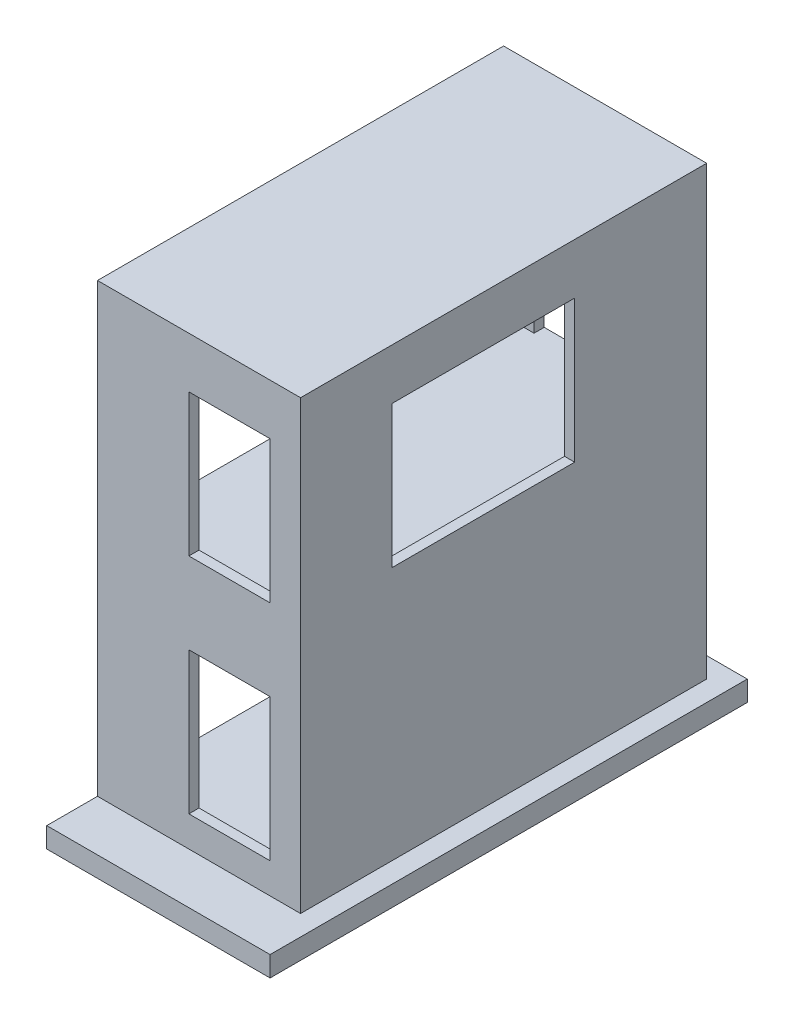
SolidWorks part; units mm, degrees
ref_plane "Front Plane" through (0, 0, 0) normal (0, 0, 1) x (1, 0, 0)
ref_plane "Top Plane" through (0, 0, 0) normal (0, 1, 0) x (1, 0, 0)
ref_plane "Right Plane" through (0, 0, 0) normal (1, 0, 0) x (0, 0, -1)
sketch "Sketch1" plane through (0, 0, 0) normal (0, 1, 0) x (1, 0, 0)
  line L1 (-60, -117.5) -> (60, -117.5)
  line L2 (-60, -117.5) -> (-60, 117.5)
  line L3 (-60, 117.5) -> (60, 117.5)
  line L4 (60, -117.5) -> (60, 117.5)
  line L5 (-60, -117.5) -> (60, 117.5) construction
  line L6 (-60, 117.5) -> (60, -117.5) construction
  point P0 (0, 0)
  dimension "D1" = 235
  dimension "D2" = 120
extrude "floor" add sketch "Sketch1" along normal blind 10
sketch "Sketch2" plane through (0, 10, 0) normal (0, 1, 0) x (1, 0, 0)
  line L0 (-50, 107.5) -> (50, 107.5) construction
  line L1 (-50, 102.5) -> (45, 102.5) construction
  line L2 (50, 107.5) -> (50, -92.5) construction
  line L3 (45, 102.5) -> (45, -87.5) construction
  line L4 (50, -92.5) -> (35, -92.5) construction
  line L5 (-5, -92.5) -> (-50, -92.5) construction
  line L6 (45, -87.5) -> (35, -87.5) construction
  line L7 (-5, -87.5) -> (-50, -87.5) construction
  line L8 (45, -87.5) -> (35, -87.5) construction
  line L9 (35, -87.5) -> (35, -92.5) construction
  line L10 (-5, -92.5) -> (-5, -87.5) construction
  line L11 (-50, -92.5) -> (50, 107.5) construction
  line L12 (-50, 102.5) -> (-50, 107.5)
  line L13 (-50, -92.5) -> (-50, -87.5) construction
  line L14 (-50, 107.5) -> (50, 107.5)
  line L15 (-50, 107.5) -> (50, -92.5) construction
  line L16 (50, 107.5) -> (50, -92.5)
  line L17 (50, -92.5) -> (35, -92.5)
  line L18 (35, -92.5) -> (35, -87.5)
  line L19 (35, -87.5) -> (45, -87.5)
  line L20 (45, -87.5) -> (45, 102.5)
  line L21 (45, 102.5) -> (-50, 102.5)
  line L22 (-50, -87.5) -> (-50, -92.5)
  line L23 (-50, -92.5) -> (-5, -92.5)
  line L24 (-5, -92.5) -> (-5, -87.5)
  line L25 (-5, -87.5) -> (-50, -87.5)
  line L26 (60, -117.5) -> (60, 117.5) construction
  dimension "D1" = 10
  dimension "D2" = 15
  dimension "D3" = 25
  dimension "D4" = 65
  dimension "D5" = 110
  dimension "D6" = 10
  dimension "D7" = 15
  dimension "D8" = 205
extrude "Boss-Extrude2" add sketch "Sketch2" along normal blind 100
ref_plane "Plane2" through (0, 110, 0) normal (0, 1, 0) x (1, 0, 0)
sketch "Sketch3" plane through (0, 110, 0) normal (0, 1, 0) x (1, 0, 0)
  line L0 (50, 107.5) -> (50, -92.5)
  line L1 (50, -92.5) -> (-50, -92.5)
  line L2 (-50, -92.5) -> (-50, 107.5)
  line L3 (-50, 107.5) -> (50, 107.5)
  dimension "D1" = 200
extrude "Boss-Extrude3" add sketch "Sketch3" along normal blind 10
sketch "Sketch4" plane through (0, 120, 0) normal (0, 1, 0) x (1, 0, 0)
  line L0 (-50, 107.5) -> (50, 107.5) construction
  line L1 (-50, 102.5) -> (45, 102.5) construction
  line L2 (50, 107.5) -> (50, 42.5) construction
  line L3 (50, -47.5) -> (50, -92.5) construction
  line L4 (45, 102.5) -> (45, 42.5) construction
  line L5 (45, -47.5) -> (45, -87.5) construction
  line L6 (50, -92.5) -> (35, -92.5) construction
  line L7 (-5, -87.5) -> (-50, -87.5) construction
  line L8 (35, -87.5) -> (35, -92.5) construction
  line L9 (-5, -92.5) -> (-5, -87.5) construction
  line L10 (-50, -92.5) -> (-5, -92.5) construction
  line L11 (35, -87.5) -> (45, -87.5) construction
  line L12 (45, 42.5) -> (50, 42.5) construction
  line L13 (45, -47.5) -> (50, -47.5) construction
  line L14 (-50, 107.5) -> (50, -92.5) construction
  line L15 (-50, -92.5) -> (50, 107.5) construction
  line L16 (-50, 102.5) -> (-50, 107.5)
  line L17 (-50, 107.5) -> (50, 107.5)
  line L18 (50, 107.5) -> (50, 42.5)
  line L19 (50, 42.5) -> (45, 42.5)
  line L20 (45, 42.5) -> (45, 102.5)
  line L21 (45, 102.5) -> (-50, 102.5)
  line L22 (-50, -92.5) -> (-50, -87.5)
  line L23 (-50, -87.5) -> (-5, -87.5)
  line L24 (-5, -87.5) -> (-5, -92.5)
  line L25 (-5, -92.5) -> (-50, -92.5)
  line L26 (35, -87.5) -> (35, -92.5)
  line L27 (35, -92.5) -> (50, -92.5)
  line L28 (50, -92.5) -> (50, -47.5)
  line L29 (50, -47.5) -> (45, -47.5)
  line L30 (45, -47.5) -> (45, -87.5)
  line L31 (45, -87.5) -> (35, -87.5)
  line L32 (-50, 107.5) -> (-50, -92.5) construction
  line L33 (50, 107.5) -> (-50, 107.5) construction
  dimension "D1" = 45
  dimension "D2" = 85
  dimension "D3" = 95
  dimension "D4" = 100
  dimension "D5" = 65
  dimension "D6" = 155
extrude "Boss-Extrude4" add sketch "Sketch4" along normal blind 100
ref_plane "Plane4" through (0, 220, 0) normal (0, 1, 0) x (1, 0, 0)
sketch "Sketch5" plane through (0, 220, 0) normal (0, 1, 0) x (1, 0, 0)
  line L0 (-50, 107.5) -> (50, 107.5)
  line L1 (50, 107.5) -> (50, -92.5)
  line L2 (50, -92.5) -> (-50, -92.5)
  line L3 (-50, -92.5) -> (-50, 107.5)
  dimension "D1" = 200
extrude "Boss-Extrude5" add sketch "Sketch5" along normal blind 10
sketch "Sketch6" plane through (0, 0, 92.5) normal (0, 0, 1) x (1, 0, 0)
  line L0 (35, 10) -> (35, 25)
  line L1 (35, 110) -> (35, 10) construction
  line L2 (35, 25) -> (-5, 25)
  line L3 (-5, 110) -> (-5, 10) construction
  line L4 (-5, 25) -> (-5, 10)
  line L5 (-60, 10) -> (60, 10) construction
  line L6 (-5, 10) -> (35, 10)
  line L7 (-5, 110) -> (-5, 95)
  line L8 (-5, 95) -> (35, 95)
  line L9 (35, 95) -> (35, 110)
  line L10 (35, 110) -> (-5, 110)
  line L11 (-5, 120) -> (-5, 135)
  line L12 (-5, 220) -> (-5, 120) construction
  line L13 (-5, 135) -> (35, 135)
  line L14 (35, 220) -> (35, 120) construction
  line L15 (35, 135) -> (35, 120)
  line L16 (35, 120) -> (-5, 120)
  line L17 (-5, 220) -> (-5, 205)
  line L18 (-5, 205) -> (35, 205)
  line L19 (35, 205) -> (35, 220)
  line L20 (-5, 220) -> (35, 220) construction
  line L21 (-50, 220) -> (45, 220) construction
  line L22 (35, 220) -> (-5, 220)
  dimension "D1" = 15
  dimension "D2" = 15
  dimension "D3" = 15
  dimension "D4" = 15
extrude "Boss-Extrude6" add sketch "Sketch6" against normal blind 5
sketch "Sketch7" plane through (50, 0, 0) normal (1, 0, 0) x (0, 0, -1)
  line L0 (-47.5, 120) -> (-47.5, 135)
  line L1 (-47.5, 220) -> (-47.5, 120) construction
  line L2 (-47.5, 135) -> (42.5, 135)
  line L3 (42.5, 220) -> (42.5, 120) construction
  line L4 (42.5, 135) -> (42.5, 120)
  line L5 (42.5, 120) -> (-47.5, 120)
  line L6 (-47.5, 220) -> (-47.5, 205)
  line L7 (-47.5, 205) -> (42.5, 205)
  line L8 (42.5, 205) -> (42.5, 220)
  line L9 (-47.5, 220) -> (42.5, 220) construction
  line L10 (42.5, 220) -> (-47.5, 220)
  dimension "D1" = 15
  dimension "D2" = 15
extrude "Boss-Extrude7" add sketch "Sketch7" against normal blind 5
sketch "Sketch8" plane through (0, 0, -107.5) normal (0, 0, -1) x (-1, 0, 0)
  line L0 (50, 10) -> (50, 110) construction
  line L1 (50, 230) -> (50, 10) construction
  line L2 (50, 110) -> (-50, 110) construction
  line L3 (-50, 230) -> (-50, 10) construction
  line L4 (-50, 110) -> (-50, 120) construction
  line L5 (-50, 120) -> (50, 120) construction
  line L6 (50, 120) -> (50, 230) construction
  line L7 (50, 110) -> (-50, 10) construction
  line L8 (-50, 120) -> (50, 230) construction
  line L9 (-50, 110) -> (50, 10) construction
  line L10 (-60, 10) -> (60, 10) construction
  line L11 (-50, 230) -> (50, 120) construction
  line L12 (-30, 90) -> (30, 90)
  line L13 (-30, 90) -> (-30, 10)
  line L14 (-30, 10) -> (30, 10)
  line L15 (30, 90) -> (30, 10)
  line L16 (-30, 90) -> (30, 10) construction
  line L17 (-30, 10) -> (30, 90) construction
  line L18 (-30, 120) -> (30, 120)
  line L19 (-30, 200) -> (30, 200)
  line L20 (30, 200) -> (30, 120)
  line L21 (-30, 200) -> (-30, 120)
  line L22 (-50, 10) -> (50, 10) construction
  point P5 (0, 50)
  dimension "D1" = 100
  dimension "D2" = 10
  dimension "D3" = 80
  dimension "D4" = 60
  dimension "D5" = 20
extrude "Cut-Extrude1" cut sketch "Sketch8" against normal blind 5
sketch "Sketch10" plane through (0, 10, 0) normal (0, 1, 0) x (1, 0, 0)
  line L0 (-60, -117.5) -> (60, -117.5) construction
  line L1 (-60, 117.5) -> (-50, 117.5)
  line L2 (-60, 117.5) -> (-60, -117.5)
  line L3 (-60, -117.5) -> (-50, -117.5)
  line L4 (-50, 117.5) -> (-50, -117.5)
  dimension "D1" = 10
extrude "Cut-Extrude2" cut sketch "Sketch10" against normal blind 10
ref_plane "Plane5" through (50, 230, -107.5) normal (0, -1, 0) x (-1, 0, 0)
equation "\"D2@Sketch6\"=\"D1@Sketch6\""
equation "\"D3@Sketch6\"=\"D1@Sketch6\""
equation "\"D4@Sketch6\"=\"D1@Sketch6\""
equation "\"D1@Sketch7\"=\"D1@Sketch6\""
equation "\"D2@Sketch7\"=\"D1@Sketch6\""
